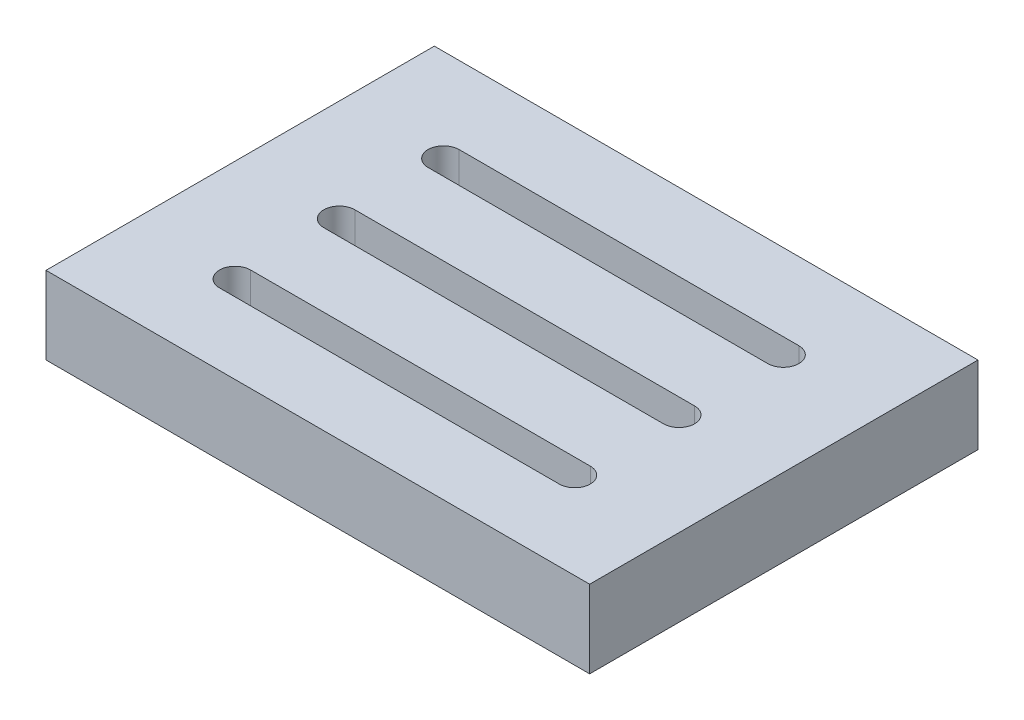
SolidWorks part; units mm, degrees
ref_plane "Front Plane" through (0, 0, 0) normal (0, 0, 1) x (1, 0, 0)
ref_plane "Top Plane" through (0, 0, 0) normal (0, 1, 0) x (1, 0, 0)
ref_plane "Right Plane" through (0, 0, 0) normal (1, 0, 0) x (0, 0, -1)
sketch "Sketch1" plane through (0, 0, 0) normal (0, 1, 0) x (1, 0, 0)
  line L1 (-35, 25) -> (35, 25)
  line L2 (-35, 25) -> (-35, -25)
  line L3 (-35, -25) -> (35, -25)
  line L4 (35, 25) -> (35, -25)
  line L5 (-35, 25) -> (35, -25) construction
  line L6 (-35, -25) -> (35, 25) construction
  point P0 (0, 0)
  dimension "D1" = 50
  dimension "D2" = 70
extrude "Boss-Extrude1" add sketch "Sketch1" along normal blind 10
sketch "Sketch2" plane through (0, 10, 0) normal (0, 1, 0) x (1, 0, 0)
  line L0 (-21.8712, 13.0643) -> (21.8712, 13.0643) construction
  line L1 (-21.8712, 13.0643) -> (21.8712, 13.0643) construction
  line L2 (-21.8712, 13.0643) -> (-21.8712, -13.7911) construction
  line L3 (-21.8712, -13.7911) -> (21.8712, -13.7911) construction
  line L4 (21.8712, 13.0643) -> (21.8712, -13.7911) construction
  line L5 (-21.8712, 15.0643) -> (21.8712, 15.0643)
  line L6 (-21.8712, 11.0643) -> (21.8712, 11.0643)
  line L7 (-21.8712, -13.7911) -> (21.8712, -13.7911) construction
  line L8 (-21.8712, -11.7911) -> (21.8712, -11.7911)
  line L9 (-21.8712, -15.7911) -> (21.8712, -15.7911)
  line L10 (-21.8712, -0.3634) -> (21.8712, -0.3634) construction
  line L11 (-21.8712, 1.6366) -> (21.8712, 1.6366)
  line L12 (-21.8712, -2.3634) -> (21.8712, -2.3634)
  arc A0 (-21.8712, 15.0643) -> (-21.8712, 11.0643) centre (-21.8712, 13.0643) ccw
  arc A1 (21.8712, 11.0643) -> (21.8712, 15.0643) centre (21.8712, 13.0643) ccw
  arc A2 (-21.8712, -11.7911) -> (-21.8712, -15.7911) centre (-21.8712, -13.7911) ccw
  arc A3 (21.8712, -15.7911) -> (21.8712, -11.7911) centre (21.8712, -13.7911) ccw
  arc A4 (-21.8712, 1.6366) -> (-21.8712, -2.3634) centre (-21.8712, -0.3634) ccw
  arc A5 (21.8712, -2.3634) -> (21.8712, 1.6366) centre (21.8712, -0.3634) ccw
  point P0 (0, 0)
  point P6 (0, 13.0643)
  point P11 (0, -13.7911)
  point P18 (0, -0.3634)
  dimension "D1" = 2
  dimension "D2" = 2
  dimension "D3" = 2
extrude "Cut-Extrude1" cut sketch "Sketch2" against normal blind 10
